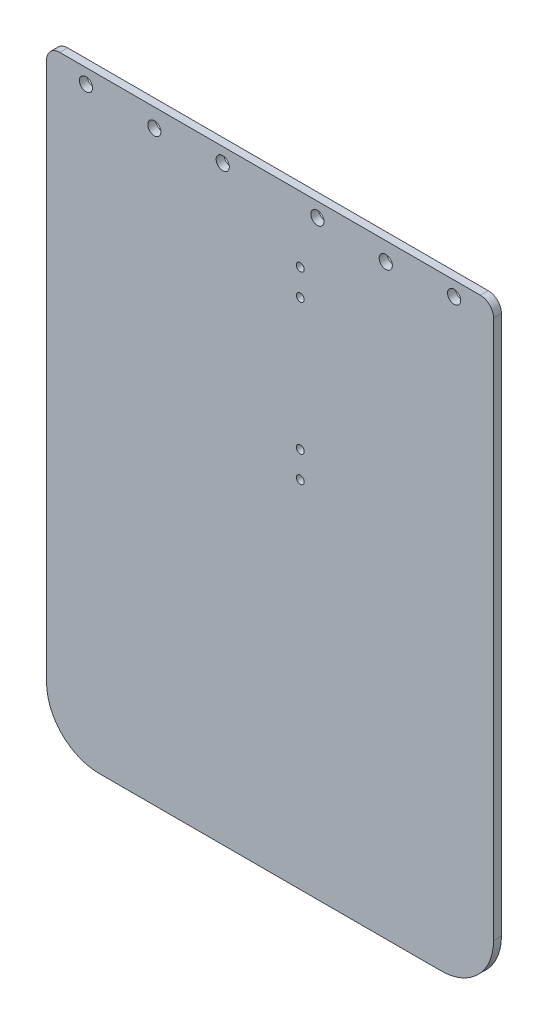
SolidWorks part; units mm, degrees
ref_plane "前视基准面" through (0, 0, 0) normal (0, 0, 1) x (1, 0, 0)
ref_plane "上视基准面" through (0, 0, 0) normal (0, 1, 0) x (1, 0, 0)
ref_plane "右视基准面" through (0, 0, 0) normal (1, 0, 0) x (0, 0, -1)
sketch "草图1" plane through (0, 0, 0) normal (0, 0, 1) x (1, 0, 0)
  line L1 (-85, 100) -> (85, 100)
  line L2 (-85, 100) -> (-85, -100)
  line L3 (-85, -100) -> (85, -100)
  line L4 (85, 100) -> (85, -100)
  line L5 (-85, 100) -> (85, -100) construction
  line L6 (-85, -100) -> (85, 100) construction
  point P0 (0, 0)
  dimension "D1" = 170
  dimension "D2" = 200
extrude "凸台-拉伸1" add sketch "草图1" along normal blind 3
sketch "草图4" plane through (0, 0, 0) normal (0, 0, -1) x (-1, 0, 0)
  line L1 (-85, -100) -> (85, -100)
  line L2 (-85, -100) -> (-85, -130)
  line L3 (-85, -130) -> (85, -130)
  line L4 (85, -100) -> (85, -130)
  dimension "D1" = 30
  dimension "D2" = 170
extrude "凸台-拉伸2" add sketch "草图4" against normal up to surface (3 mm away) up to face at (0, 0, 3)
fillet "圆角1" radius 20 2 edges at (85, -130, 1.5) (-85, -130, 1.5)
fillet "圆角2" radius 5 2 edges at (85, 100, 1.5) (-85, 100, 1.5)
sketch "草图6" plane through (0, 0, 3) normal (0, 0, 1) x (1, 0, 0)
  circle A0 centre (11.5, 5) radius 1.5
  circle A1 centre (11.5, 15) radius 1.5
  circle A2 centre (11.5, 65) radius 1.5
  circle A3 centre (11.5, 75) radius 1.5
  dimension "D1" = 3
  dimension "D2" = 3
  dimension "D3" = 3
  dimension "D4" = 3
extrude "切除-拉伸3" cut sketch "草图6" against normal through all
sketch "草图7" plane through (0, 0, 0) normal (0, 0, -1) x (-1, 0, 0)
  line L0 (0, 16.3525) -> (0, 116.9258) construction
  line L1 (-80, 100) -> (80, 100) construction
  line L2 (-18, 94.5) -> (-70, 94.5) construction
  line L3 (-44, 94.5) -> (-44, 80.3557) construction
  circle A0 centre (-18, 94.5) radius 2.5
  circle A1 centre (-70, 94.5) radius 2.5
  circle A2 centre (-44, 93) radius 2.5
  circle A3 centre (70, 94.5) radius 2.5
  circle A4 centre (44, 93) radius 2.5
  circle A5 centre (18, 94.5) radius 2.5
  dimension "D1" = 5.5
  dimension "D2" = 18
  dimension "D3" = 52
  dimension "D4" = 7
extrude "切除-拉伸4" cut sketch "草图7" against normal blind 10
